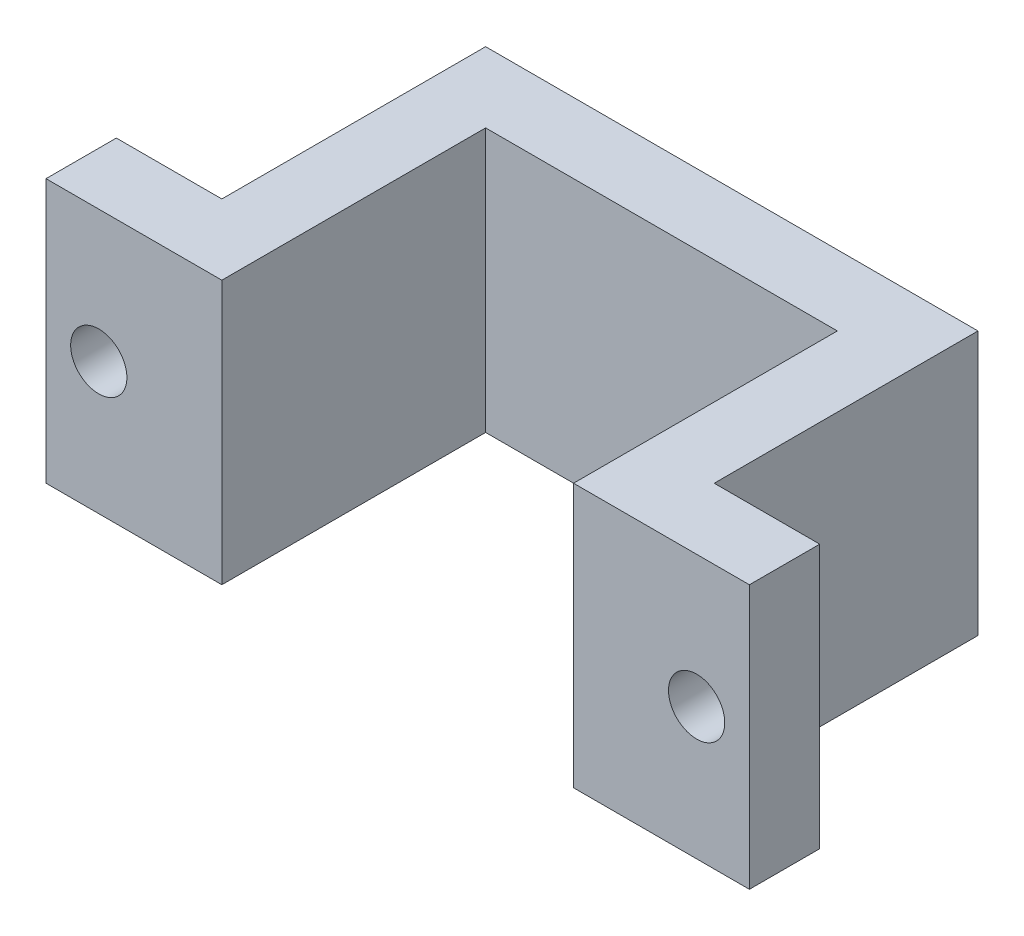
SolidWorks part; units mm, degrees
ref_plane "Front Plane" through (0, 0, 0) normal (0, 0, 1) x (1, 0, 0)
ref_plane "Top Plane" through (0, 0, 0) normal (0, 1, 0) x (1, 0, 0)
ref_plane "Right Plane" through (0, 0, 0) normal (1, 0, 0) x (0, 0, -1)
sketch "Sketch1" plane through (0, 0, 0) normal (0, 1, 0) x (1, 0, 0)
  line L0 (0, 0) -> (6.35, 0)
  line L1 (6.35, 0) -> (6.35, 9.525)
  line L2 (6.35, 9.525) -> (19.05, 9.525)
  line L3 (19.05, 9.525) -> (19.05, 0)
  line L4 (19.05, 0) -> (25.4, 0)
  line L5 (0, 2.54) -> (3.81, 2.54)
  line L6 (3.81, 2.54) -> (3.81, 12.065)
  line L7 (3.81, 12.065) -> (21.59, 12.065)
  line L8 (21.59, 12.065) -> (21.59, 2.54)
  line L9 (21.59, 2.54) -> (25.4, 2.54)
  line L10 (0, 0) -> (0, 2.54)
  line L11 (25.4, 0) -> (25.4, 2.54)
  dimension "D1" = 6.35
  dimension "D2" = 12.7
  dimension "D3" = 9.525
  dimension "D4" = 2.54
extrude "Boss-Extrude1" add sketch "Sketch1" along normal blind 9.525
sketch "Sketch2" plane through (0, 0, -2.54) normal (0, 0, -1) x (-1, 0, 0)
  line L0 (0, 4.7625) -> (-25.4, 4.7625) construction
  line L1 (0, 9.525) -> (0, 0) construction
  line L2 (-25.4, 9.525) -> (-25.4, 0) construction
  line L3 (-1.905, 0) -> (-1.905, 9.525) construction
  line L4 (-3.81, 0) -> (0, 0) construction
  line L5 (-3.81, 9.525) -> (0, 9.525) construction
  line L6 (-23.495, 0) -> (-23.495, 9.525) construction
  line L7 (-25.4, 0) -> (-21.59, 0) construction
  line L8 (-25.4, 9.525) -> (-21.59, 9.525) construction
  circle A0 centre (-1.905, 4.7625) radius 1.016
  circle A1 centre (-23.495, 4.7625) radius 1.016
  dimension "D1" = 2.032
  dimension "D2" = 2.032
extrude "Cut-Extrude1" cut sketch "Sketch2" against normal up to next
